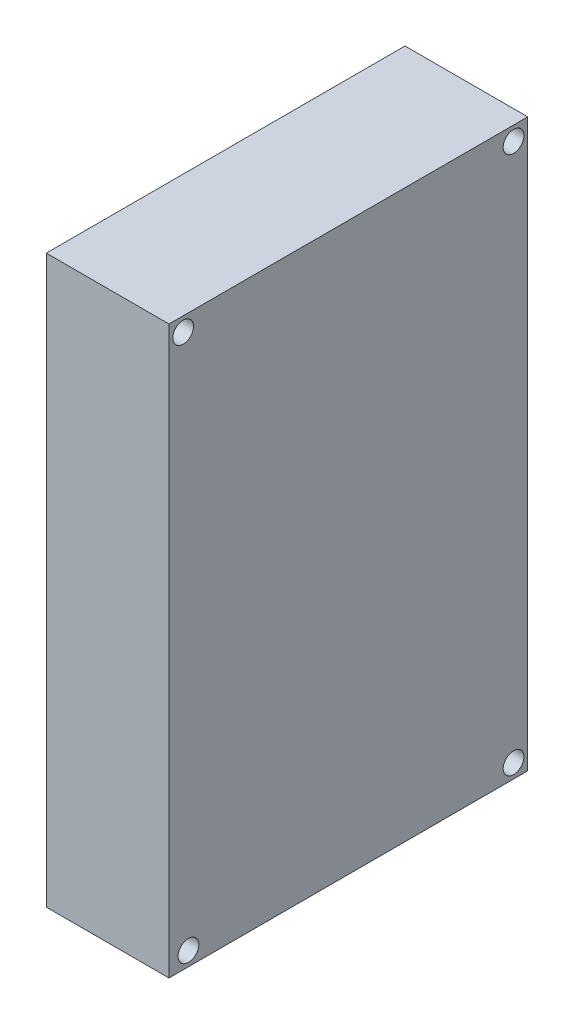
SolidWorks part; units mm, degrees
material "FR4"
ref_plane "Front Plane" through (0, 0, 0) normal (0, 0, 1) x (1, 0, 0)
ref_plane "Top Plane" through (0, 0, 0) normal (0, 1, 0) x (1, 0, 0)
ref_plane "Right Plane" through (0, 0, 0) normal (1, 0, 0) x (0, 0, -1)
sketch "Sketch1" plane through (0, 0, 0) normal (0, 0, 1) x (1, 0, 0)
  line L1 (-6.5, 30) -> (6.5, 30)
  line L2 (-6.5, 30) -> (-6.5, -30)
  line L3 (-6.5, -30) -> (6.5, -30)
  line L4 (6.5, 30) -> (6.5, -30)
  line L5 (-6.5, 30) -> (6.5, -30) construction
  line L6 (-6.5, -30) -> (6.5, 30) construction
  point P0 (0, 0)
  dimension "D1" = 60
  dimension "D2" = 13
extrude "Boss-Extrude1" add sketch "Sketch1" along normal blind 38
sketch "Sketch2" plane through (6.5, 0, 0) normal (1, 0, 0) x (0, 0, -1)
  line L0 (-38, -30) -> (0, -30) construction
  line L1 (-38, -30) -> (-38, 30) construction
  line L2 (0, -30) -> (0, 30) construction
  circle A0 centre (-1.5, 28.4972) radius 1.1
  circle A1 centre (-36.5, 28.4972) radius 1.1
  circle A2 centre (-35.9388, -28.5) radius 1.1
  circle A3 centre (-1.5, -28.5) radius 1.1
  dimension "D1" = 57
  dimension "D2" = 1.5
  dimension "D3" = 1.5
  dimension "D4" = 1.5
extrude "Cut-Extrude1" cut sketch "Sketch2" against normal through all
